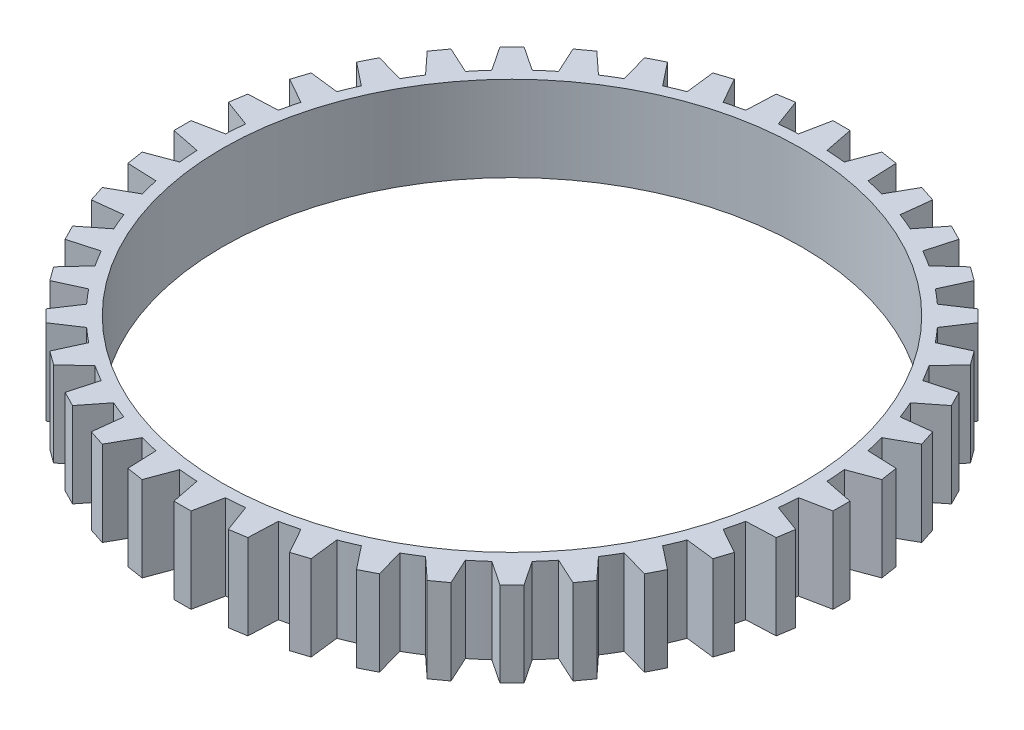
SolidWorks part; units mm, degrees
ref_plane "Front Plane" through (0, 0, 0) normal (0, 0, 1) x (1, 0, 0)
ref_plane "Top Plane" through (0, 0, 0) normal (0, 1, 0) x (1, 0, 0)
ref_plane "Right Plane" through (0, 0, 0) normal (1, 0, 0) x (0, 0, -1)
sketch "Sketch1" plane through (0, 0, 0) normal (0, 1, 0) x (1, 0, 0)
  line L1 (-2.5119, 52.9404) -> (-1.5, 58)
  line L2 (10.7627, 51.8957) -> (10.5547, 57.0513)
  line L3 (2.5119, 52.9404) -> (1.5, 58)
  line L4 (1.5, 58) -> (-1.5, 58)
  line L5 (10.5547, 57.0513) -> (7.5917, 57.5206)
  line L6 (5.8007, 52.6816) -> (7.5917, 57.5206)
  line L7 (18.7485, 49.5731) -> (19.3496, 54.6978)
  line L8 (19.3496, 54.6978) -> (16.4964, 55.6248)
  line L9 (13.9705, 51.1256) -> (16.4964, 55.6248)
  line L10 (26.2726, 46.0299) -> (27.668, 50.9974)
  line L11 (27.668, 50.9974) -> (24.9949, 52.3594)
  line L12 (21.7963, 48.3107) -> (24.9949, 52.3594)
  line L13 (33.1498, 41.3533) -> (35.3051, 46.0413)
  line L14 (35.3051, 46.0413) -> (32.878, 47.8047)
  line L15 (29.0854, 44.3062) -> (32.878, 47.8047)
  line L16 (39.2107, 35.6584) -> (42.0729, 39.9515)
  line L17 (42.0729, 39.9515) -> (39.9515, 42.0729)
  line L18 (35.6584, 39.2107) -> (39.9515, 42.0729)
  line L19 (44.3062, 29.0854) -> (47.8047, 32.878)
  line L20 (47.8047, 32.878) -> (46.0413, 35.3051)
  line L21 (41.3533, 33.1498) -> (46.0413, 35.3051)
  line L22 (48.3107, 21.7963) -> (52.3594, 24.9949)
  line L23 (52.3594, 24.9949) -> (50.9974, 27.668)
  line L24 (46.0299, 26.2726) -> (50.9974, 27.668)
  line L25 (51.1256, 13.9705) -> (55.6248, 16.4964)
  line L26 (55.6248, 16.4964) -> (54.6978, 19.3496)
  line L27 (49.5731, 18.7485) -> (54.6978, 19.3496)
  line L28 (52.6816, 5.8007) -> (57.5206, 7.5917)
  line L29 (57.5206, 7.5917) -> (57.0513, 10.5547)
  line L30 (51.8957, 10.7627) -> (57.0513, 10.5547)
  line L31 (52.9404, -2.5119) -> (58, -1.5)
  line L32 (58, -1.5) -> (58, 1.5)
  line L33 (52.9404, 2.5119) -> (58, 1.5)
  line L34 (51.8957, -10.7627) -> (57.0513, -10.5547)
  line L35 (57.0513, -10.5547) -> (57.5206, -7.5917)
  line L36 (52.6816, -5.8007) -> (57.5206, -7.5917)
  line L37 (49.5731, -18.7485) -> (54.6978, -19.3496)
  line L38 (54.6978, -19.3496) -> (55.6248, -16.4964)
  line L39 (51.1256, -13.9705) -> (55.6248, -16.4964)
  line L40 (46.0299, -26.2726) -> (50.9974, -27.668)
  line L41 (50.9974, -27.668) -> (52.3594, -24.9949)
  line L42 (48.3107, -21.7963) -> (52.3594, -24.9949)
  line L43 (41.3533, -33.1498) -> (46.0413, -35.3051)
  line L44 (46.0413, -35.3051) -> (47.8047, -32.878)
  line L45 (44.3062, -29.0854) -> (47.8047, -32.878)
  line L46 (35.6584, -39.2107) -> (39.9515, -42.0729)
  line L47 (39.9515, -42.0729) -> (42.0729, -39.9515)
  line L48 (39.2107, -35.6584) -> (42.0729, -39.9515)
  line L49 (29.0854, -44.3062) -> (32.878, -47.8047)
  line L50 (32.878, -47.8047) -> (35.3051, -46.0413)
  line L51 (33.1498, -41.3533) -> (35.3051, -46.0413)
  line L52 (21.7963, -48.3107) -> (24.9949, -52.3594)
  line L53 (24.9949, -52.3594) -> (27.668, -50.9974)
  line L54 (26.2726, -46.0299) -> (27.668, -50.9974)
  line L55 (13.9705, -51.1256) -> (16.4964, -55.6248)
  line L56 (16.4964, -55.6248) -> (19.3496, -54.6978)
  line L57 (18.7485, -49.5731) -> (19.3496, -54.6978)
  line L58 (5.8007, -52.6816) -> (7.5917, -57.5206)
  line L59 (7.5917, -57.5206) -> (10.5547, -57.0513)
  line L60 (10.7627, -51.8957) -> (10.5547, -57.0513)
  line L61 (-2.5119, -52.9404) -> (-1.5, -58)
  line L62 (-1.5, -58) -> (1.5, -58)
  line L63 (2.5119, -52.9404) -> (1.5, -58)
  line L64 (-10.7627, -51.8957) -> (-10.5547, -57.0513)
  line L65 (-10.5547, -57.0513) -> (-7.5917, -57.5206)
  line L66 (-5.8007, -52.6816) -> (-7.5917, -57.5206)
  line L67 (-18.7485, -49.5731) -> (-19.3496, -54.6978)
  line L68 (-19.3496, -54.6978) -> (-16.4964, -55.6248)
  line L69 (-13.9705, -51.1256) -> (-16.4964, -55.6248)
  line L70 (-26.2726, -46.0299) -> (-27.668, -50.9974)
  line L71 (-27.668, -50.9974) -> (-24.9949, -52.3594)
  line L72 (-21.7963, -48.3107) -> (-24.9949, -52.3594)
  line L73 (-33.1498, -41.3533) -> (-35.3051, -46.0413)
  line L74 (-35.3051, -46.0413) -> (-32.878, -47.8047)
  line L75 (-29.0854, -44.3062) -> (-32.878, -47.8047)
  line L76 (-39.2107, -35.6584) -> (-42.0729, -39.9515)
  line L77 (-42.0729, -39.9515) -> (-39.9515, -42.0729)
  line L78 (-35.6584, -39.2107) -> (-39.9515, -42.0729)
  line L79 (-44.3062, -29.0854) -> (-47.8047, -32.878)
  line L80 (-47.8047, -32.878) -> (-46.0413, -35.3051)
  line L81 (-41.3533, -33.1498) -> (-46.0413, -35.3051)
  line L82 (-48.3107, -21.7963) -> (-52.3594, -24.9949)
  line L83 (-52.3594, -24.9949) -> (-50.9974, -27.668)
  line L84 (-46.0299, -26.2726) -> (-50.9974, -27.668)
  line L85 (-51.1256, -13.9705) -> (-55.6248, -16.4964)
  line L86 (-55.6248, -16.4964) -> (-54.6978, -19.3496)
  line L87 (-49.5731, -18.7485) -> (-54.6978, -19.3496)
  line L88 (-52.6816, -5.8007) -> (-57.5206, -7.5917)
  line L89 (-57.5206, -7.5917) -> (-57.0513, -10.5547)
  line L90 (-51.8957, -10.7627) -> (-57.0513, -10.5547)
  line L91 (-52.9404, 2.5119) -> (-58, 1.5)
  line L92 (-58, 1.5) -> (-58, -1.5)
  line L93 (-52.9404, -2.5119) -> (-58, -1.5)
  line L94 (-51.8957, 10.7627) -> (-57.0513, 10.5547)
  line L95 (-57.0513, 10.5547) -> (-57.5206, 7.5917)
  line L96 (-52.6816, 5.8007) -> (-57.5206, 7.5917)
  line L97 (-49.5731, 18.7485) -> (-54.6978, 19.3496)
  line L98 (-54.6978, 19.3496) -> (-55.6248, 16.4964)
  line L99 (-51.1256, 13.9705) -> (-55.6248, 16.4964)
  line L100 (-46.0299, 26.2726) -> (-50.9974, 27.668)
  line L101 (-50.9974, 27.668) -> (-52.3594, 24.9949)
  line L102 (-48.3107, 21.7963) -> (-52.3594, 24.9949)
  line L103 (-41.3533, 33.1498) -> (-46.0413, 35.3051)
  line L104 (-46.0413, 35.3051) -> (-47.8047, 32.878)
  line L105 (-44.3062, 29.0854) -> (-47.8047, 32.878)
  line L106 (-35.6584, 39.2107) -> (-39.9515, 42.0729)
  line L107 (-39.9515, 42.0729) -> (-42.0729, 39.9515)
  line L108 (-39.2107, 35.6584) -> (-42.0729, 39.9515)
  line L109 (-29.0854, 44.3062) -> (-32.878, 47.8047)
  line L110 (-32.878, 47.8047) -> (-35.3051, 46.0413)
  line L111 (-33.1498, 41.3533) -> (-35.3051, 46.0413)
  line L112 (-21.7963, 48.3107) -> (-24.9949, 52.3594)
  line L113 (-24.9949, 52.3594) -> (-27.668, 50.9974)
  line L114 (-26.2726, 46.0299) -> (-27.668, 50.9974)
  line L115 (-13.9705, 51.1256) -> (-16.4964, 55.6248)
  line L116 (-16.4964, 55.6248) -> (-19.3496, 54.6978)
  line L117 (-18.7485, 49.5731) -> (-19.3496, 54.6978)
  line L118 (-5.8007, 52.6816) -> (-7.5917, 57.5206)
  line L119 (-7.5917, 57.5206) -> (-10.5547, 57.0513)
  line L120 (-10.7627, 51.8957) -> (-10.5547, 57.0513)
  arc A0 (-2.5119, 52.9404) -> (-5.8007, 52.6816) centre (0, 0) ccw
  arc A1 (-10.7627, 51.8957) -> (-13.9705, 51.1256) centre (0, 0) ccw
  arc A2 (-18.7485, 49.5731) -> (-21.7963, 48.3107) centre (0, 0) ccw
  arc A3 (5.8007, 52.6816) -> (2.5119, 52.9404) centre (0, 0) ccw
  arc A4 (13.9705, 51.1256) -> (10.7627, 51.8957) centre (0, 0) ccw
  arc A5 (-26.2726, 46.0299) -> (-29.0854, 44.3062) centre (0, 0) ccw
  arc A6 (-33.1498, 41.3533) -> (-35.6584, 39.2107) centre (0, 0) ccw
  arc A7 (-39.2107, 35.6584) -> (-41.3533, 33.1498) centre (0, 0) ccw
  arc A8 (-44.3062, 29.0854) -> (-46.0299, 26.2726) centre (0, 0) ccw
  arc A9 (-48.3107, 21.7963) -> (-49.5731, 18.7485) centre (0, 0) ccw
  arc A10 (-51.1256, 13.9705) -> (-51.8957, 10.7627) centre (0, 0) ccw
  arc A11 (-52.6816, 5.8007) -> (-52.9404, 2.5119) centre (0, 0) ccw
  arc A12 (-52.9404, -2.5119) -> (-52.6816, -5.8007) centre (0, 0) ccw
  arc A13 (-51.8957, -10.7627) -> (-51.1256, -13.9705) centre (0, 0) ccw
  arc A14 (-49.5731, -18.7485) -> (-48.3107, -21.7963) centre (0, 0) ccw
  arc A15 (-46.0299, -26.2726) -> (-44.3062, -29.0854) centre (0, 0) ccw
  arc A16 (-41.3533, -33.1498) -> (-39.2107, -35.6584) centre (0, 0) ccw
  arc A17 (-35.6584, -39.2107) -> (-33.1498, -41.3533) centre (0, 0) ccw
  arc A18 (-29.0854, -44.3062) -> (-26.2726, -46.0299) centre (0, 0) ccw
  arc A19 (-21.7963, -48.3107) -> (-18.7485, -49.5731) centre (0, 0) ccw
  arc A20 (-13.9705, -51.1256) -> (-10.7627, -51.8957) centre (0, 0) ccw
  arc A21 (-5.8007, -52.6816) -> (-2.5119, -52.9404) centre (0, 0) ccw
  arc A22 (2.5119, -52.9404) -> (5.8007, -52.6816) centre (0, 0) ccw
  arc A23 (10.7627, -51.8957) -> (13.9705, -51.1256) centre (0, 0) ccw
  arc A24 (18.7485, -49.5731) -> (21.7963, -48.3107) centre (0, 0) ccw
  arc A25 (26.2726, -46.0299) -> (29.0854, -44.3062) centre (0, 0) ccw
  arc A26 (33.1498, -41.3533) -> (35.6584, -39.2107) centre (0, 0) ccw
  arc A27 (39.2107, -35.6584) -> (41.3533, -33.1498) centre (0, 0) ccw
  arc A28 (44.3062, -29.0854) -> (46.0299, -26.2726) centre (0, 0) ccw
  arc A29 (48.3107, -21.7963) -> (49.5731, -18.7485) centre (0, 0) ccw
  arc A30 (51.1256, -13.9705) -> (51.8957, -10.7627) centre (0, 0) ccw
  arc A31 (52.6816, -5.8007) -> (52.9404, -2.5119) centre (0, 0) ccw
  arc A32 (52.9404, 2.5119) -> (52.6816, 5.8007) centre (0, 0) ccw
  arc A33 (51.8957, 10.7627) -> (51.1256, 13.9705) centre (0, 0) ccw
  arc A34 (49.5731, 18.7485) -> (48.3107, 21.7963) centre (0, 0) ccw
  arc A35 (46.0299, 26.2726) -> (44.3062, 29.0854) centre (0, 0) ccw
  arc A36 (41.3533, 33.1498) -> (39.2107, 35.6584) centre (0, 0) ccw
  arc A37 (35.6584, 39.2107) -> (33.1498, 41.3533) centre (0, 0) ccw
  arc A38 (29.0854, 44.3062) -> (26.2726, 46.0299) centre (0, 0) ccw
  arc A39 (21.7963, 48.3107) -> (18.7485, 49.5731) centre (0, 0) ccw
  point P6 (0, 53)
  dimension "D1" = 106
  dimension "D2" = 40
  dimension "D4" = 3
extrude "Boss-Extrude1" add sketch "Sketch1" along normal blind 15
sketch "Sketch4" plane through (0, 15, 0) normal (0, 1, 0) x (1, 0, 0)
  circle A0 centre (0, 0) radius 51
  dimension "D1" = 102
extrude "Cut-Extrude1" cut sketch "Sketch4" against normal through all and the other way through all
